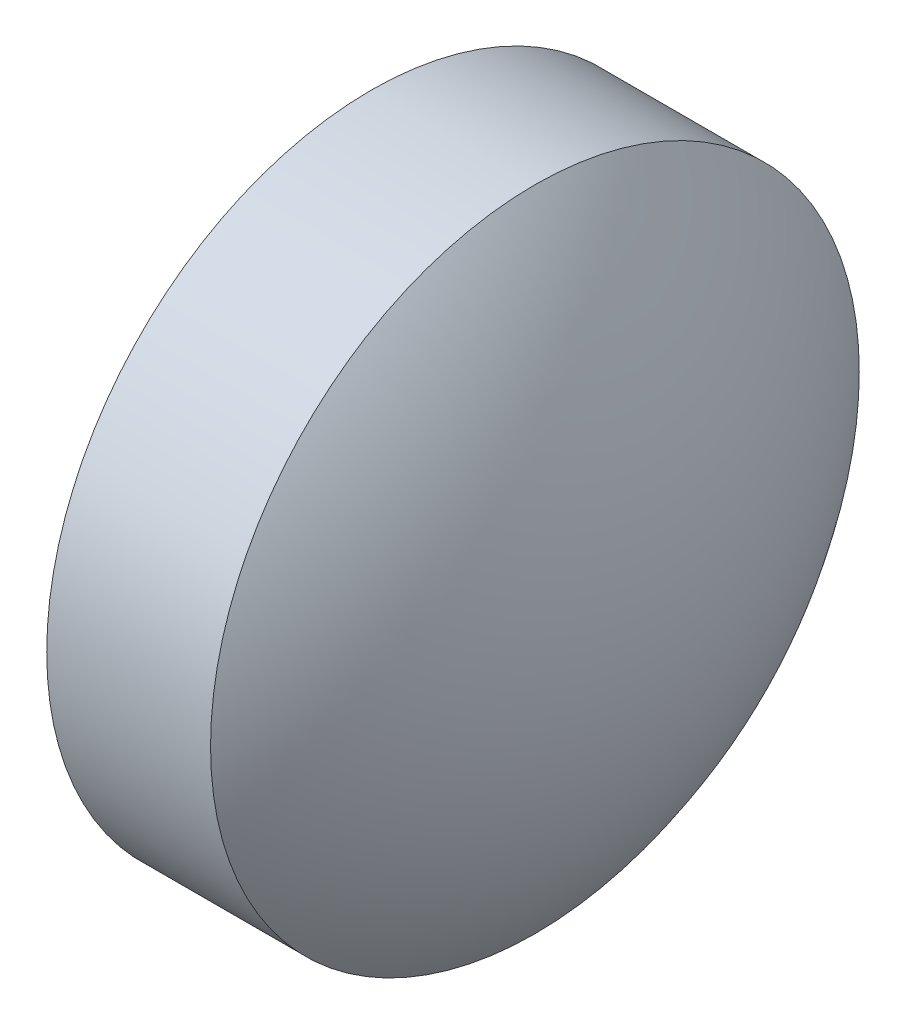
SolidWorks part; units mm, degrees
ref_plane "前视基准面" through (0, 0, 0) normal (0, 0, 1) x (1, 0, 0)
ref_plane "上视基准面" through (0, 0, 0) normal (0, 1, 0) x (1, 0, 0)
ref_plane "右视基准面" through (0, 0, 0) normal (1, 0, 0) x (0, 0, -1)
sketch "草图1" plane through (0, 0, 0) normal (0, 0, 1) x (1, 0, 0)
  line L0 (526.5312, 150.1308) -> (526.5312, 148.1308)
  line L1 (526.5312, 148.1308) -> (528.2312, 148.1308)
  line L2 (526.5312, 150.1308) -> (527.5412, 150.1308)
  line L3 (525.9013, 148.1308) -> (528.5904, 148.1308) construction
  arc A0 (528.2312, 148.1308) -> (527.5412, 150.1308) centre (524.9877, 148.1308) ccw
revolve "旋转1" add sketch "草图1" angle 360 about L3
